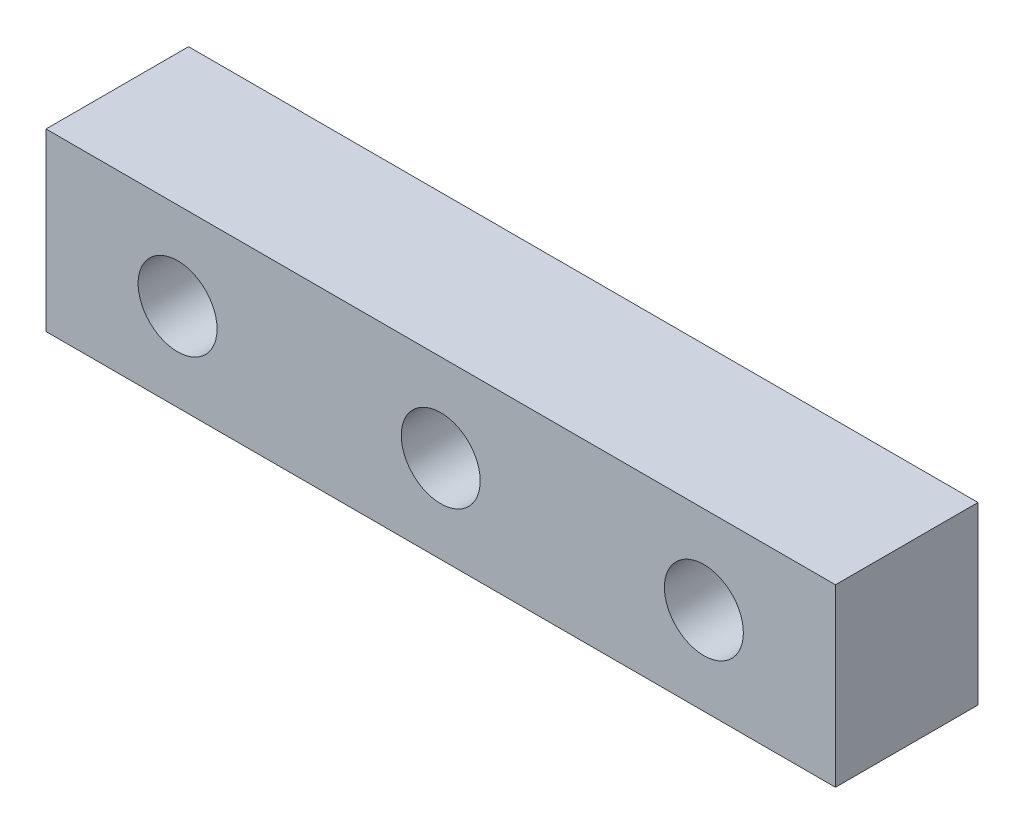
SolidWorks part; units mm, degrees
material "ABS"
ref_plane "前视基准面" through (0, 0, 0) normal (0, 0, 1) x (1, 0, 0)
ref_plane "上视基准面" through (0, 0, 0) normal (0, 1, 0) x (1, 0, 0)
ref_plane "右视基准面" through (0, 0, 0) normal (1, 0, 0) x (0, 0, -1)
sketch "草图1" plane through (0, 0, 0) normal (0, 0, 1) x (1, 0, 0)
  line L0 (-45, 0) -> (-30, 0) construction
  line L1 (-45, 10) -> (45, 10)
  line L2 (-45, 10) -> (-45, -10)
  line L3 (-45, -10) -> (45, -10)
  line L4 (45, 10) -> (45, -10)
  line L5 (-45, 10) -> (45, -10) construction
  line L6 (-45, -10) -> (45, 10) construction
  line L7 (45, 0) -> (30, 0) construction
  circle A0 centre (-30, 0) radius 4.5
  circle A1 centre (0, 0) radius 4.5
  circle A2 centre (30, 0) radius 4.5
  point P0 (0, 0)
extrude "凸台-拉伸1" add sketch "草图1" along normal blind 16.25
